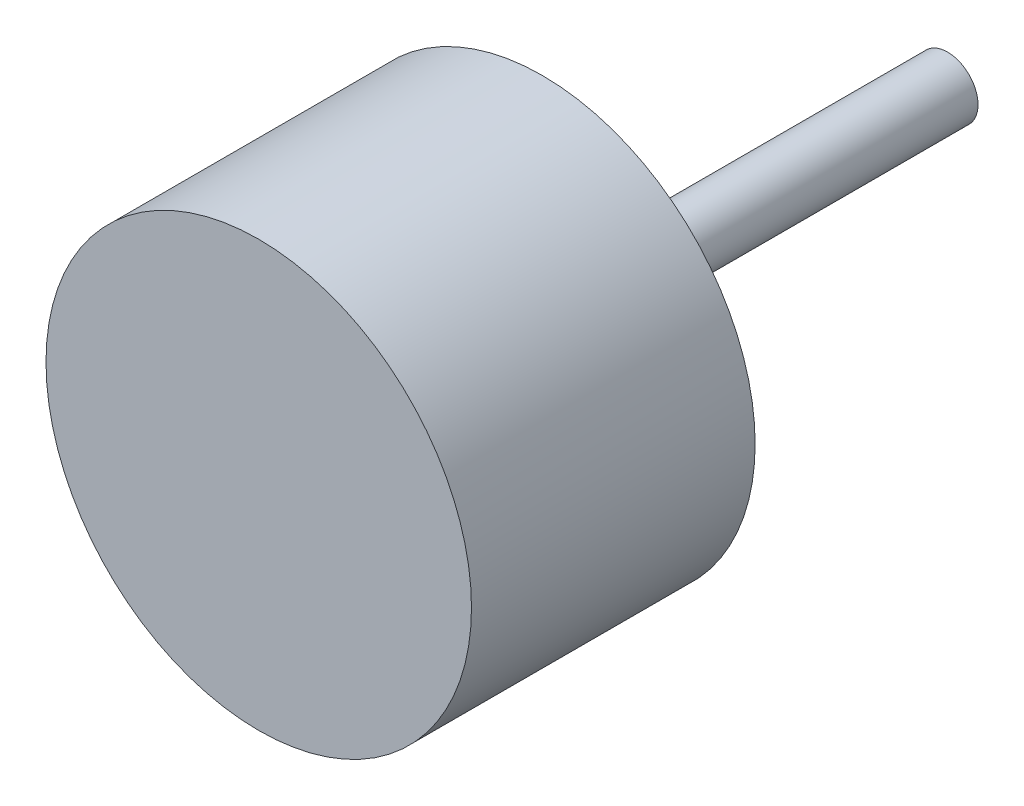
SolidWorks part; units mm, degrees
ref_plane "Plan de face" through (0, 0, 0) normal (0, 0, 1) x (1, 0, 0)
ref_plane "Plan de dessus" through (0, 0, 0) normal (0, 1, 0) x (1, 0, 0)
ref_plane "Plan de droite" through (0, 0, 0) normal (1, 0, 0) x (0, 0, -1)
sketch "Esquisse1" plane through (0, 0, 0) normal (0, 0, 1) x (1, 0, 0)
  circle A0 centre (0, 0) radius 10.5
  dimension "D1" = 21
extrude "Boss.-Extru.1" add sketch "Esquisse1" along normal blind 14
sketch "Esquisse2" plane through (0, 0, 0) normal (0, 0, -1) x (-1, 0, 0)
  circle A0 centre (0, 0) radius 1.5
  dimension "D1" = 3
extrude "Boss.-Extru.2" add sketch "Esquisse2" along normal blind 20
